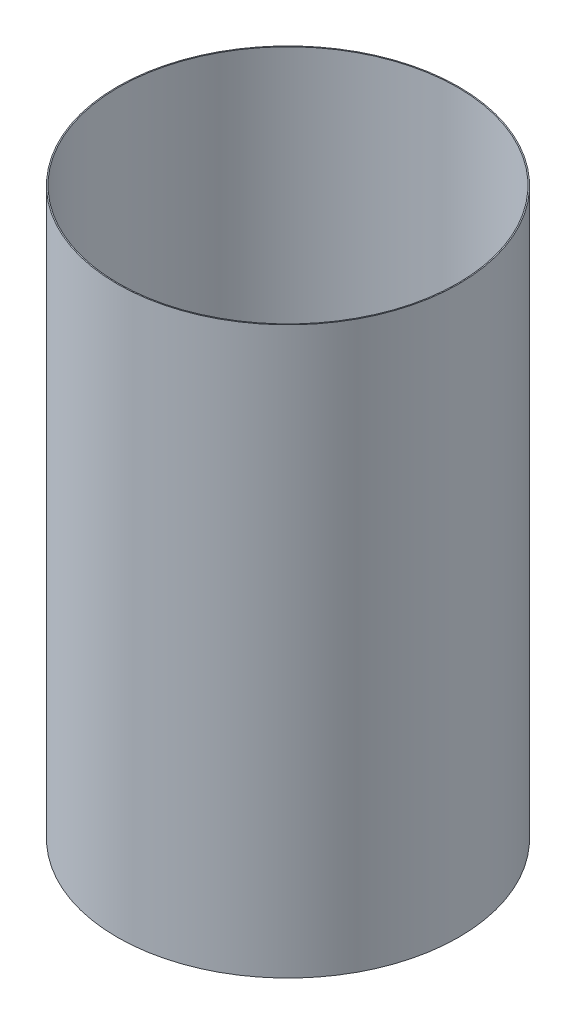
SolidWorks part; units mm, degrees
material "Thornel Mat VMA"
ref_plane "Front Plane" through (0, 0, 0) normal (0, 0, 1) x (1, 0, 0)
ref_plane "Top Plane" through (0, 0, 0) normal (0, 1, 0) x (1, 0, 0)
ref_plane "Right Plane" through (0, 0, 0) normal (1, 0, 0) x (0, 0, -1)
ref_axis "Axis1" through (0, 55, 0) along (0, -1, 0)
sketch "Sketch1" plane through (0, 0, 0) normal (0, 0, 1) x (1, 0, 0)
  line L0 (-40.005, -69.0032) -> (-40.005, -202.3532)
  line L2 (-38.1, -202.3532) -> (0, -202.3532) construction
  line L3 (-38.1, -69.0032) -> (0, -69.0032) construction
  point P2 (-39.624, -69.0032)
  point P3 (-39.624, -69.0032)
  point P4 (-40.005, -69.0032)
revolve "Revolve-Thin1" add sketch "Sketch1" angle 360 about axis through (0, 55, 0) along (0, -1, 0)
equation "\"D3@Revolve-Thin1\"=\"CF THICKNESS@Cryo Tank.Assembly\""
